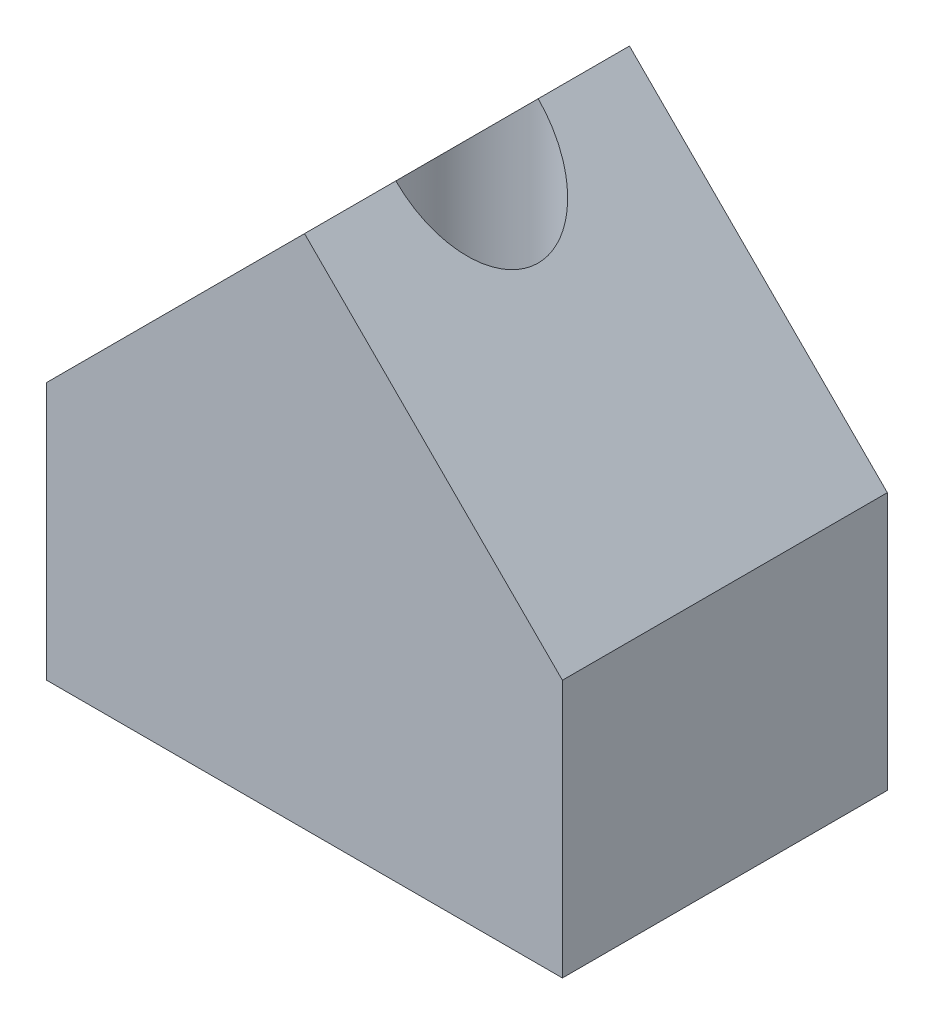
SolidWorks part; units mm, degrees
material "6061-T6 (SS)"
ref_plane "Front Plane" through (0, 0, 0) normal (0, 0, 1) x (1, 0, 0)
ref_plane "Top Plane" through (0, 0, 0) normal (0, 1, 0) x (1, 0, 0)
ref_plane "Right Plane" through (0, 0, 0) normal (1, 0, 0) x (0, 0, -1)
sketch "Sketch1" plane through (0, 0, 0) normal (0, 0, 1) x (1, 0, 0)
  line L0 (0, 6.35) -> (6.35, 0)
  line L1 (-6.35, -6.35) -> (6.35, -6.35)
  line L2 (-6.35, -6.35) -> (-6.35, 6.35)
  line L3 (-6.35, 6.35) -> (6.35, 6.35)
  line L4 (6.35, -6.35) -> (6.35, 6.35)
  line L5 (-6.35, -6.35) -> (6.35, 6.35) construction
  line L6 (-6.35, 6.35) -> (6.35, -6.35) construction
  line L7 (0, 6.35) -> (-6.35, 0)
  point P0 (0, 0)
  dimension "D1" = 12.7
  dimension "D2" = 12.7
  dimension "D3" = 90
  dimension "D4" = 45
extrude "Boss-Extrude1" add sketch "Sketch1" along normal blind 8.001 contours L0 L7 L2 L1 L4
sketch "Sketch2" plane through (0, -6.35, 0) normal (0, -1, 0) x (1, 0, 0)
  line L0 (0, 0) -> (0, 8.001) construction
  circle A0 centre (0, 4.0005) radius 1.7526
  dimension "D1" = 3.5052
extrude ".25-20 tapped hole" cut sketch "Sketch2" against normal through all
